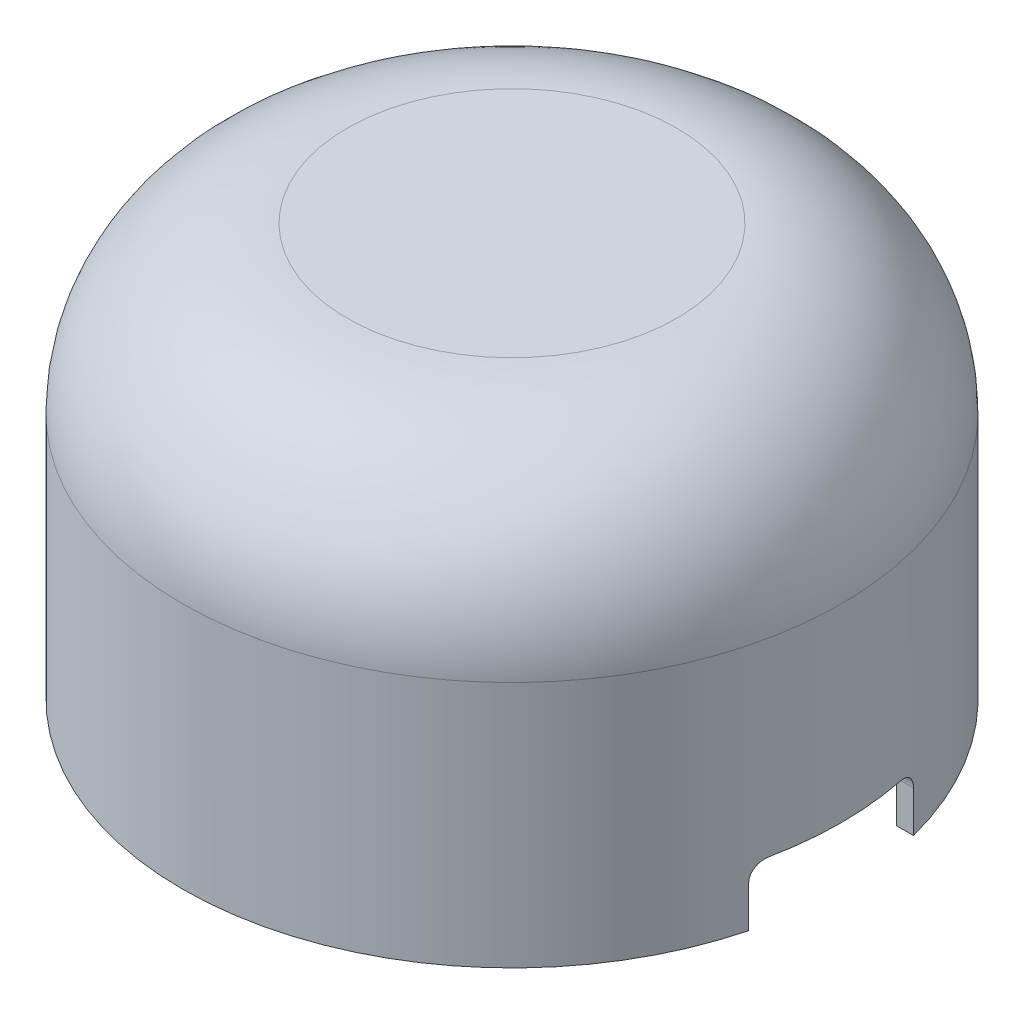
SolidWorks part; units mm, degrees
ref_plane "Front Plane" through (0, 0, 0) normal (0, 0, 1) x (1, 0, 0)
ref_plane "Top Plane" through (0, 0, 0) normal (0, 1, 0) x (1, 0, 0)
ref_plane "Right Plane" through (0, 0, 0) normal (1, 0, 0) x (0, 0, -1)
sketch "Sketch1" plane through (0, 0, 0) normal (1, 0, 0) x (0, 0, -1)
  line L0 (0, 0) -> (0, 50)
  line L1 (0, 50) -> (20, 50)
  line L3 (40, 30) -> (40, 0)
  line L4 (0, 0) -> (40, 0)
  arc A0 (40, 30) -> (20, 50) centre (20, 30) ccw
  dimension "D2" = 20
  dimension "D1" = 50
  dimension "D3" = 30
  dimension "D4" = 20
revolve "Revolve1" add sketch "Sketch1" angle 360 about L0
shell "Shell1" thickness 2
sketch "Sketch2" plane through (0, 48, 0) normal (0, -1, 0) x (1, 0, 0)
  circle A0 centre (0, 0) radius 2.5
  dimension "D1" = 5
extrude "Boss-Extrude1" add sketch "Sketch2" along normal blind 55
ref_plane "Plane1" through (6, 0, 0) normal (1, 0, 0) x (0, 0, -1)
sketch "Sketch3" plane through (6, 0, 0) normal (1, 0, 0) x (0, 0, -1)
  line L0 (-10, 0) -> (10, 0)
  line L1 (-40, 0) -> (40, 0) construction
  line L2 (-10, 0) -> (-10, 5)
  line L3 (-8, 7) -> (8, 7)
  line L4 (10, 5) -> (10, 0)
  arc A0 (8, 7) -> (10, 5) centre (8, 5) cw
  arc A1 (-10, 5) -> (-8, 7) centre (-8, 5) cw
  point P5 (0, 0)
  point P12 (-10, 7)
  dimension "D3" = 2
  dimension "D1" = 20
  dimension "D2" = 7
extrude "Cut-Extrude2" cut sketch "Sketch3" along normal blind 50
